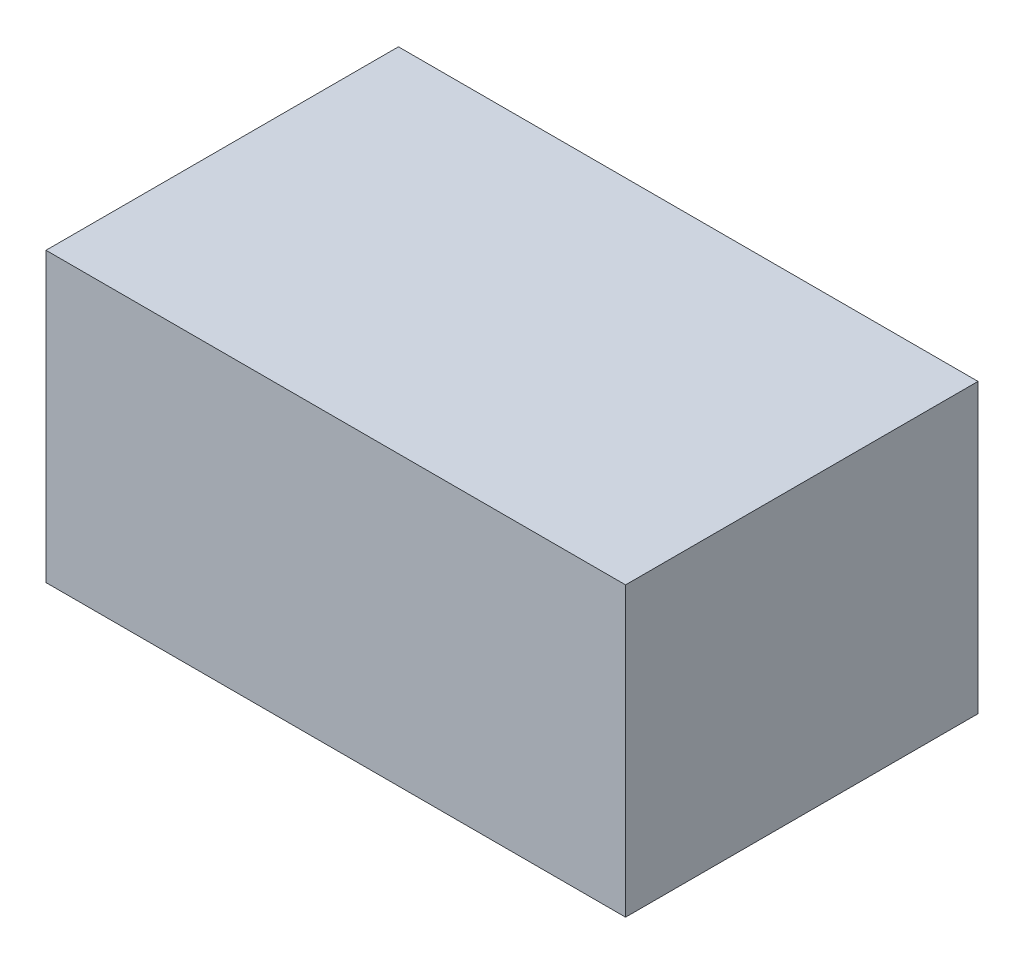
SolidWorks part; units mm, degrees
ref_plane "Front Plane" through (0, 0, 0) normal (0, 0, 1) x (1, 0, 0)
ref_plane "Top Plane" through (0, 0, 0) normal (0, 1, 0) x (1, 0, 0)
ref_plane "Right Plane" through (0, 0, 0) normal (1, 0, 0) x (0, 0, -1)
sketch "Sketch1" plane through (0, 0, 0) normal (0, 0, 1) x (1, 0, 0)
  line L1 (0, 0) -> (14.8, 0)
  line L2 (0, 0) -> (0, 7.35)
  line L3 (0, 7.35) -> (14.8, 7.35)
  line L4 (14.8, 0) -> (14.8, 7.35)
  dimension "D1" = 14.8
  dimension "D2" = 7.35
extrude "Main" add sketch "Sketch1" along normal blind 9
